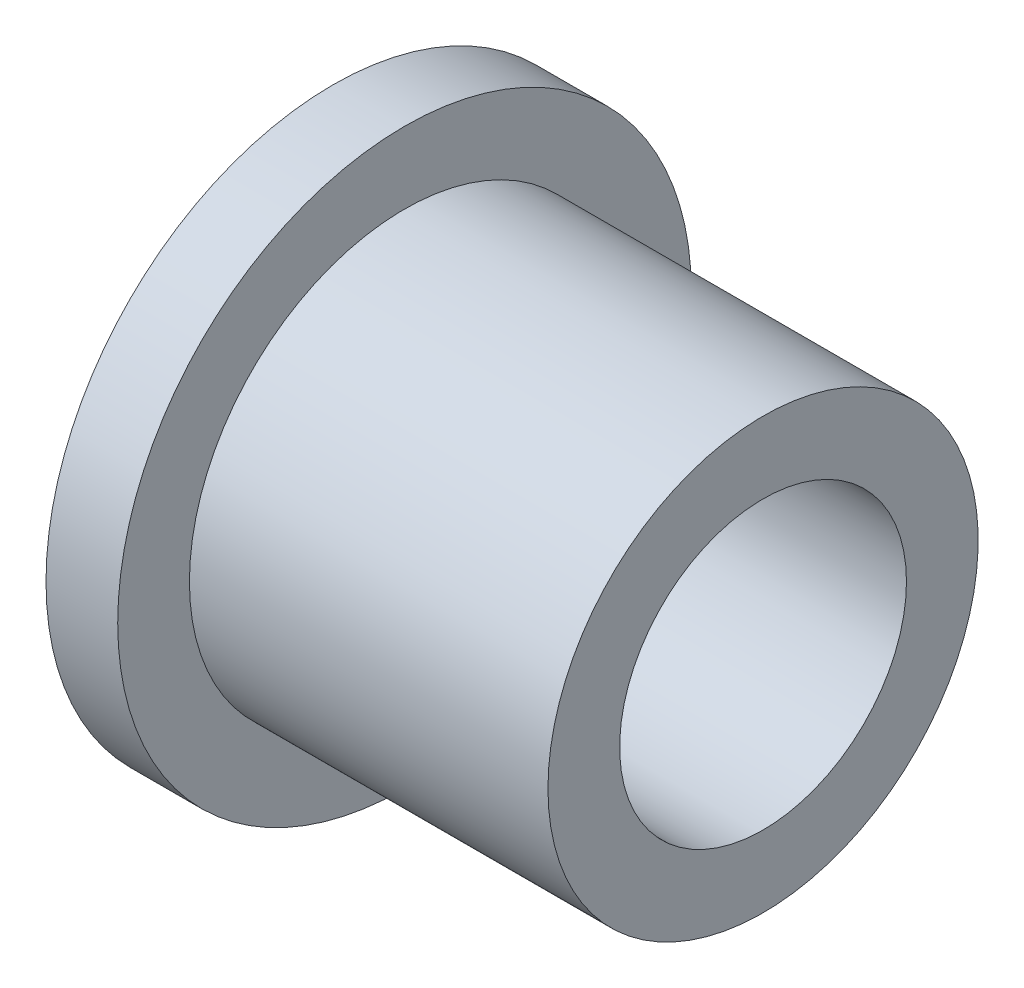
SolidWorks part; units mm, degrees
material "Manganese Bronze"
ref_plane "Front Plane" through (0, 0, 0) normal (0, 0, 1) x (1, 0, 0)
ref_plane "Top Plane" through (0, 0, 0) normal (0, 1, 0) x (1, 0, 0)
ref_plane "Right Plane" through (0, 0, 0) normal (1, 0, 0) x (0, 0, -1)
sketch "Sketch1" plane through (0, 0, 0) normal (0, 0, 1) x (1, 0, 0)
  line L0 (0, 0) -> (9.525, 0) construction
  line L1 (0, 0) -> (0, 6.35)
  line L2 (0, 6.35) -> (1.5875, 6.35)
  line L3 (1.5875, 6.35) -> (1.5875, 4.7625)
  line L4 (1.5875, 4.7625) -> (9.525, 4.7625)
  line L5 (9.525, 4.7625) -> (9.525, 0)
  line L6 (0, 0) -> (9.525, 0)
  dimension "D1" = 9.525
  dimension "D2" = 12.7
  dimension "D3" = 9.525
  dimension "D4" = 1.5875
revolve "Revolve1" add sketch "Sketch1" angle 360 about L6
sketch "Sketch2" plane through (9.525, 0, 0) normal (1, 0, 0) x (0, 0, -1)
  circle A0 centre (0, 0) radius 3.175
  dimension "D1" = 6.35
extrude "Extrude1" cut sketch "Sketch2" against normal through all
